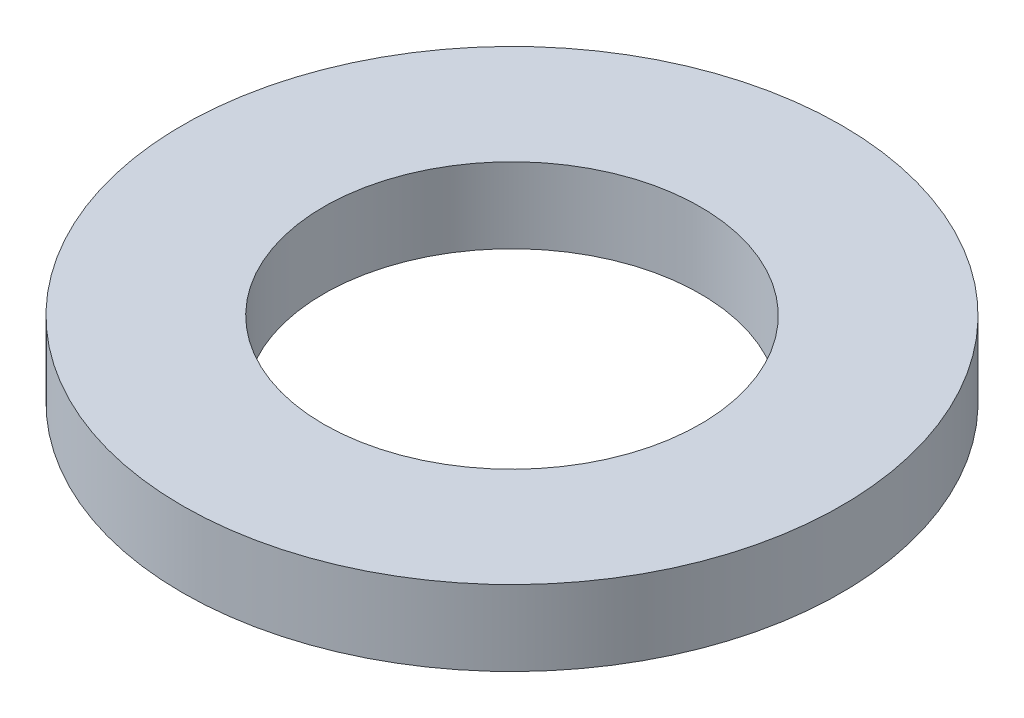
SolidWorks part; units mm, degrees
ref_plane "Front Plane" through (0, 0, 0) normal (0, 0, 1) x (1, 0, 0)
ref_plane "Top Plane" through (0, 0, 0) normal (0, 1, 0) x (1, 0, 0)
ref_plane "Right Plane" through (0, 0, 0) normal (1, 0, 0) x (0, 0, -1)
sketch "Sketch1" plane through (0, 0, 0) normal (0, 1, 0) x (1, 0, 0)
  circle A0 centre (0, 0) radius 2.5
  circle A1 centre (0, 0) radius 4.375
  dimension "D1" = 5
  dimension "D2" = 8.75
extrude "Boss-Extrude1" add sketch "Sketch1" along normal blind 1
